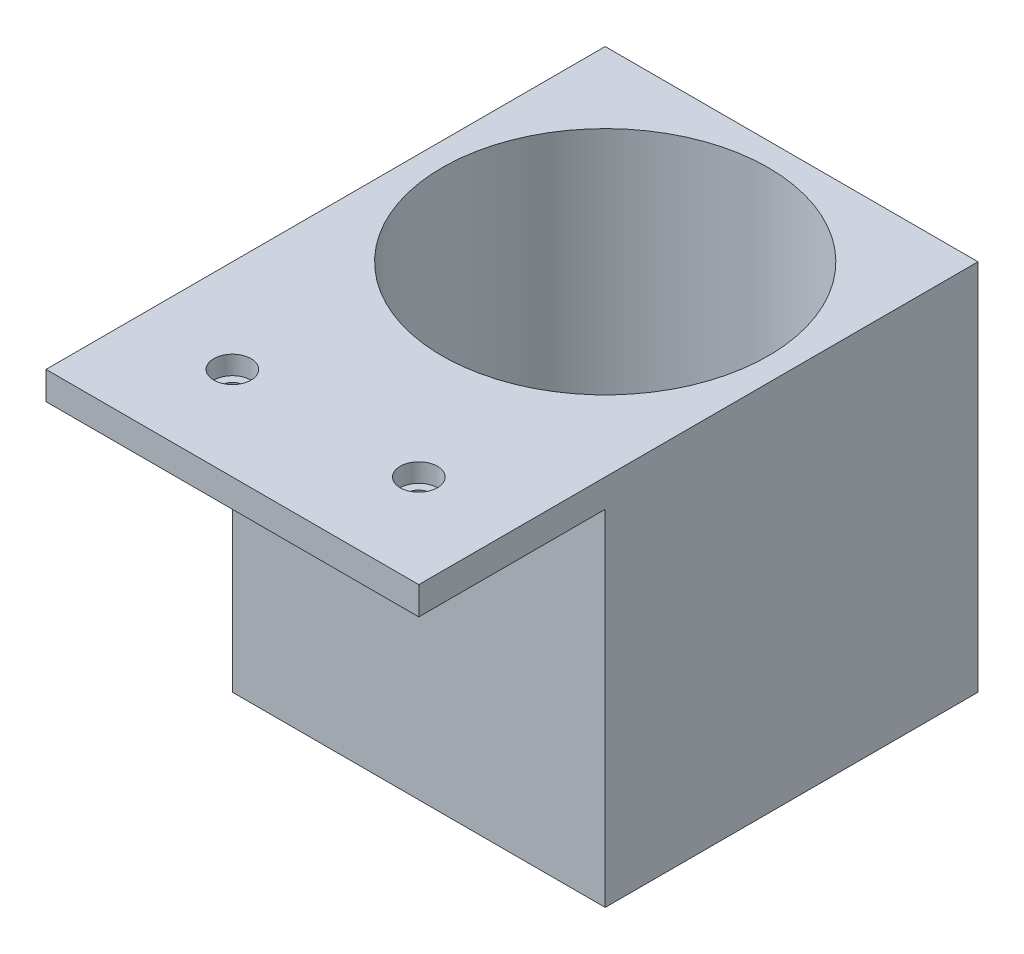
SolidWorks part; units mm, degrees
ref_plane "Front Plane" through (0, 0, 0) normal (0, 0, 1) x (1, 0, 0)
ref_plane "Top Plane" through (0, 0, 0) normal (0, 1, 0) x (1, 0, 0)
ref_plane "Right Plane" through (0, 0, 0) normal (1, 0, 0) x (0, 0, -1)
sketch "Sketch1" plane through (0, 0, 0) normal (1, 0, 0) x (0, 0, -1)
  line L0 (0, -40) -> (0, 0)
  line L1 (0, 0) -> (-40, 0)
  point P3 (0, 0)
  dimension "D1" = 40
  dimension "D2" = 40
extrude "Extrude-Thin1" add sketch "Sketch1" along normal blind 80 thin
sketch "Sketch4" plane through (0, 6, 0) normal (0, 1, 0) x (1, 0, 0)
  line L0 (80, 6) -> (80, -40) construction
  line L1 (0, 0) -> (80, 0)
  line L2 (0, 0) -> (0, 80)
  line L3 (0, 80) -> (80, 80)
  line L4 (80, 0) -> (80, 80)
  point P5 (0, 0)
  point P9 (0, 0)
  dimension "D1" = 80
extrude "Boss-Extrude1" add sketch "Sketch4" against normal blind 80
sketch "Sketch5" plane through (0, 6, 0) normal (0, 1, 0) x (1, 0, 0)
  line L0 (80, 40) -> (0, 40) construction
  line L4 (0, 80) -> (0, 0)
  line L5 (80, 80) -> (0, 80)
  line L6 (80, 0) -> (80, 80)
  line L7 (0, 0) -> (80, 0)
  line L8 (0, 80) -> (0, 0) construction
  line L9 (80, 80) -> (0, 80) construction
  line L10 (80, 0) -> (80, 80) construction
  line L11 (0, 0) -> (80, 0) construction
  circle A0 centre (40, 40) radius 35
  dimension "D2" = 70
  dimension "D1" = 0
extrude "Cut-Extrude1" cut sketch "Sketch5" against normal offset from surface 6 and the other way through all up to face at (40, -74, -40)
sketch "Sketch6" plane through (0, 6, 0) normal (0, 1, 0) x (1, 0, 0)
  line L0 (0, -20) -> (80, -20) construction
  line L1 (0, 80) -> (0, -40) construction
  line L2 (80, 80) -> (80, -40) construction
  line L3 (80, -40) -> (0, -40) construction
  point P8 (20, -20)
  point P10 (60, -20)
  dimension "D1" = 20
  dimension "D2" = 20
  dimension "D3" = 20
hole_wizard "CBORE for M4 SHCS1" positions "Sketch6" profile "Sketch7" counterbore size "M4" standard "ANSI Metric" end condition up to next
sketch "Sketch7" plane through (60, 6, 20) normal (1, 0, 0) x (0, 0, 1)
  line L0 (0, 0) -> (0, 6)
  line L1 (0, 6) -> (2.25, 6)
  line L3 (2.25, 6) -> (2.25, 4)
  line L4 (2.25, 4) -> (4, 4)
  line L5 (4, 4) -> (4, 0)
  line L7 (4, 0) -> (0, 0)
  line L11 (0, -6.35) -> (0, 107.95) construction
  dimension "Thru Hole Dia." = 4.5
  dimension "Thru Hole Depth" = 6
  dimension "C'Bore Dia." = 8
  dimension "C'Bore Depth" = 4
